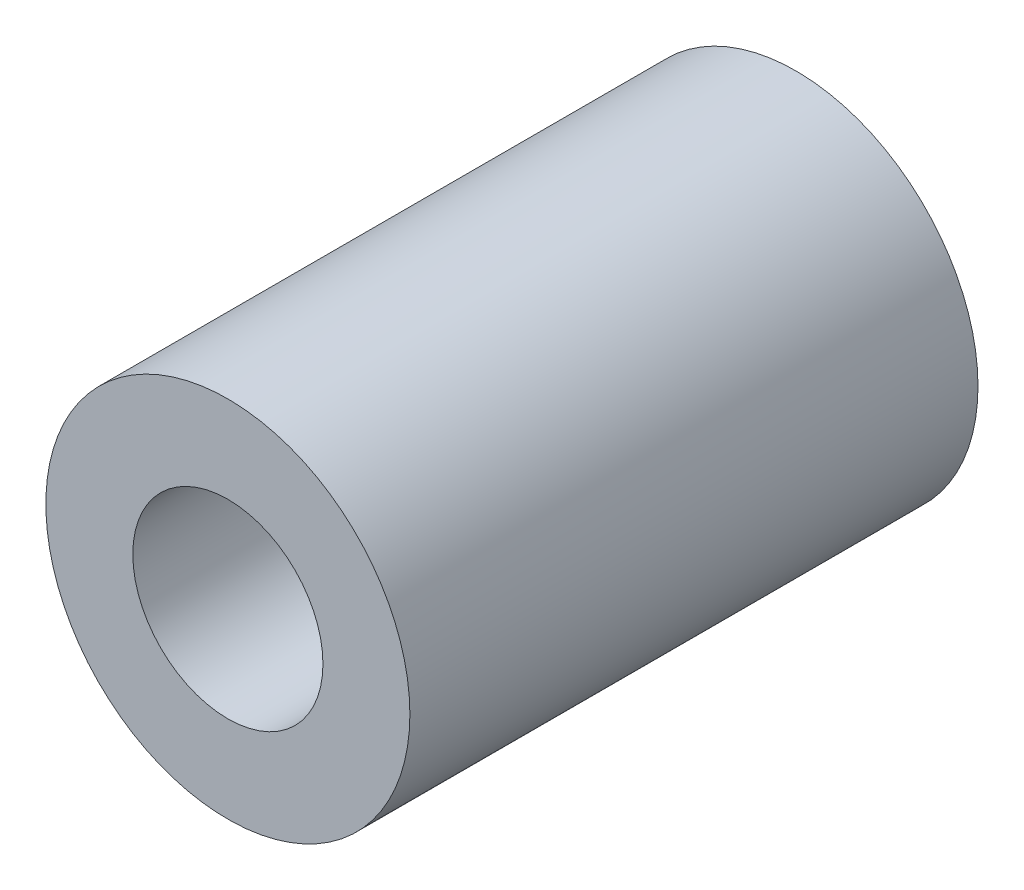
SolidWorks part; units mm, degrees
ref_plane "Front Plane" through (0, 0, 0) normal (0, 0, 1) x (1, 0, 0)
ref_plane "Top Plane" through (0, 0, 0) normal (0, 1, 0) x (1, 0, 0)
ref_plane "Right Plane" through (0, 0, 0) normal (1, 0, 0) x (0, 0, -1)
sketch "Sketch1" plane through (0, 0, 0) normal (0, 0, 1) x (1, 0, 0)
  circle A0 centre (0, 0) radius 4.1
  circle A1 centre (0, 0) radius 7.85
extrude "Boss-Extrude1" add sketch "Sketch1" along normal blind 24.5
